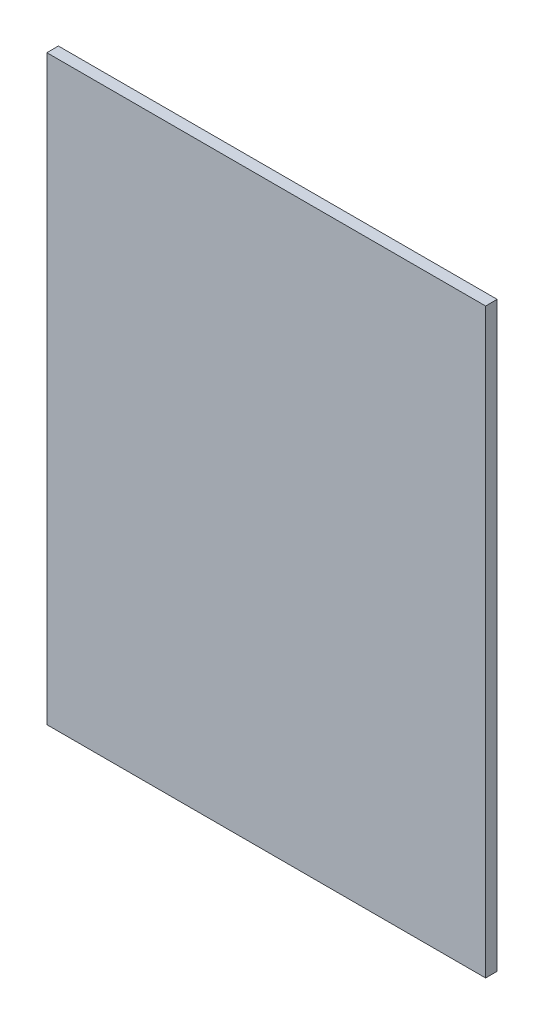
SolidWorks part; units mm, degrees
material "ABS PC"
ref_plane "Plan de face" through (0, 0, 0) normal (0, 0, 1) x (1, 0, 0)
ref_plane "Plan de dessus" through (0, 0, 0) normal (0, 1, 0) x (1, 0, 0)
ref_plane "Plan de droite" through (0, 0, 0) normal (1, 0, 0) x (0, 0, -1)
sketch "Esquisse1" plane through (0, 0, 0) normal (0, 0, 1) x (1, 0, 0)
  line L1 (130, 31.2) -> (320, 31.2)
  line L2 (130, 31.2) -> (130, -220.8)
  line L3 (130, -220.8) -> (320, -220.8)
  line L4 (320, 31.2) -> (320, -220.8)
  line L5 (307, 31.2) -> (7, 31.2) construction
  line L6 (307, -220.8) -> (65.8, -220.8) construction
  line L7 (320, 23.2) -> (320, -221.5153) construction
extrude "Boss.-Extru.1" add sketch "Esquisse1" along normal blind 5
